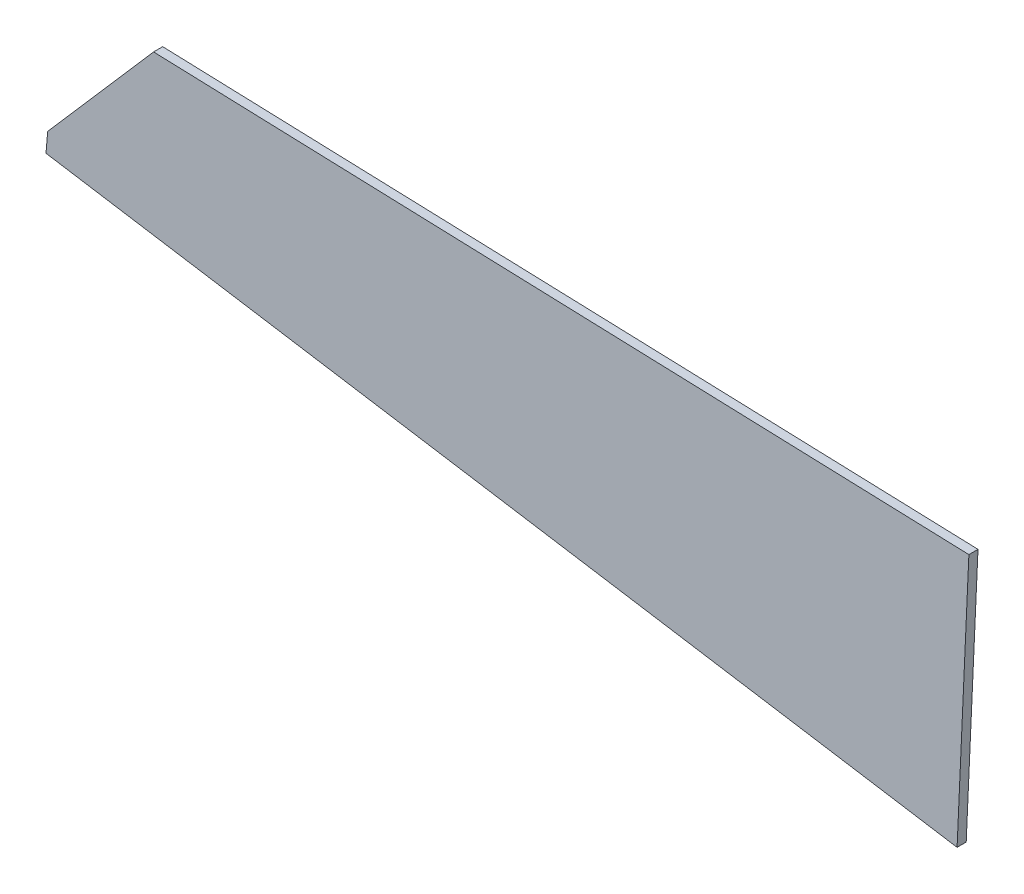
SolidWorks part; units mm, degrees
ref_plane "Plan de face" through (0, 0, 0) normal (0, 0, 1) x (1, 0, 0)
ref_plane "Plan de dessus" through (0, 0, 0) normal (0, 1, 0) x (1, 0, 0)
ref_plane "Plan de droite" through (0, 0, 0) normal (1, 0, 0) x (0, 0, -1)
sketch "Esquisse1" plane through (0, 0, 0) normal (0, 0, 1) x (1, 0, 0)
  line L1 (215.4748, 90.1482) -> (480.7658, 81.1386)
  line L2 (480.7658, 81.1386) -> (483.7658, 81.0367)
  line L9 (180.0777, 43.5565) -> (477.0025, -3.8783) construction
  line L12 (180.6403, 50.1054) -> (215.4748, 90.1482)
  line L14 (180.6403, 50.1054) -> (180.0777, 43.5565)
  line L15 (180.0777, 43.5565) -> (479.8821, -4.3384)
  line L16 (479.8821, -4.3384) -> (483.7658, 81.0367)
  line L17 (480.7658, 81.1386) -> (476.9196, -3.8651) construction
  point P2 (486.3065, 120.4932)
  point P3 (488.0482, 37.4075)
  point P5 (0, 0)
  point P7 (488.8154, 120.5618)
  point P8 (0, 0)
  point P9 (0, 0)
  point P10 (495.7864, 789.8668)
  point P11 (500.8376, 758.5751)
  point P14 (502.9053, 747.5986)
  point P15 (504.8729, 737.7189)
  point P18 (513.6324, 699.7105)
  point P19 (541.2267, 393.8931)
  point P20 (548.2712, 311.1012)
  point P21 (548.4057, 241.0884)
  point P22 (485.044, 133.1312)
  point P24 (484.4186, 129.7466)
  point P25 (0, 0)
  point P26 (476.8459, -4.3266)
  dimension "D1" = 3
  dimension "D2" = 3
extrude "Boss.-Extru.1" add sketch "Esquisse1" along normal blind 3
